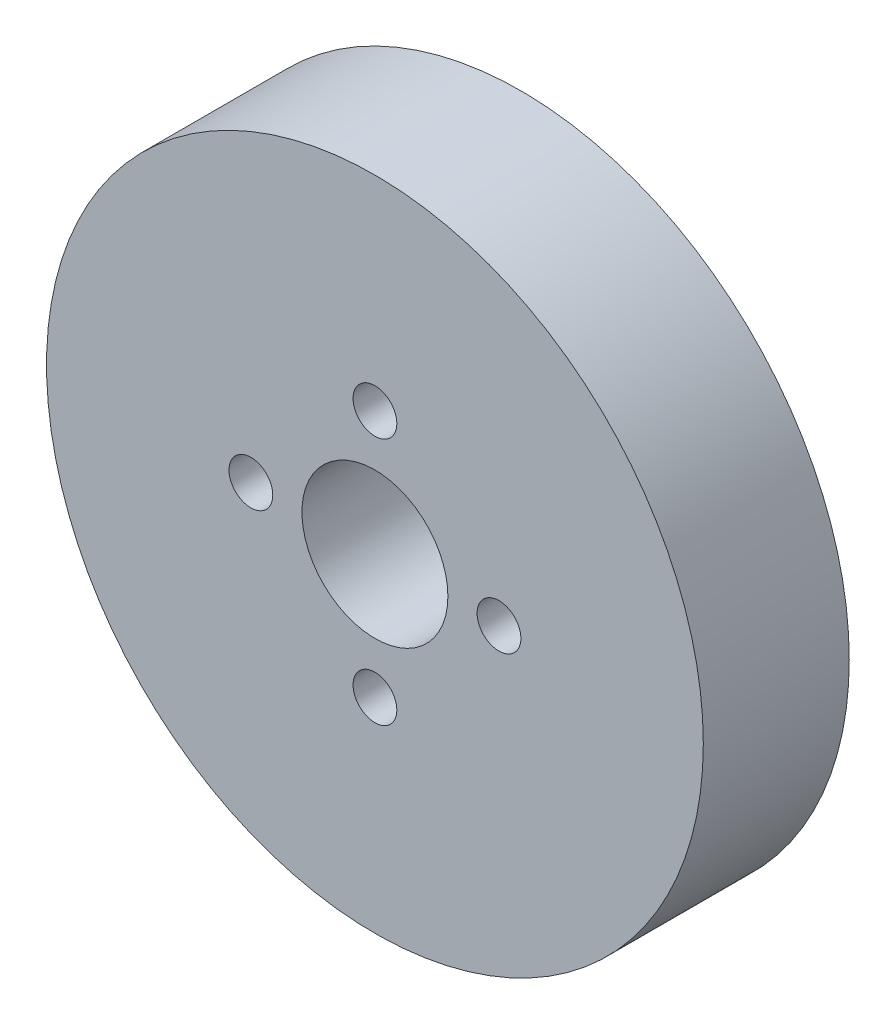
SolidWorks part; units mm, degrees
ref_plane "Plan de face" through (0, 0, 0) normal (0, 0, 1) x (1, 0, 0)
ref_plane "Plan de dessus" through (0, 0, 0) normal (0, 1, 0) x (1, 0, 0)
ref_plane "Plan de droite" through (0, 0, 0) normal (1, 0, 0) x (0, 0, -1)
sketch "Esquisse1" plane through (0, 0, 0) normal (0, 0, 1) x (1, 0, 0)
  circle A0 centre (0, 0) radius 22.5
  circle A1 centre (0, 0) radius 5
  dimension "D1" = 10
  dimension "D2" = 45
extrude "Boss.-Extru.1" add sketch "Esquisse1" along normal blind 10
hole_wizard "Dégagement M21" positions "Esquisse4" profile "Esquisse3" size "M2" standard "ISO" slot yes end condition through all
sketch "Esquisse4" plane through (0, 0, 10) normal (0, 0, 1) x (1, 0, 0)
  point P0 (0, 8.5)
  point P7 (8.5, 0)
  point P8 (0, -8.5)
  point P9 (-8.5, 0)
  point P10 (0, 0)
  dimension "D1" = 8.5
  dimension "D2" = 4
sketch "Esquisse3" plane through (0, 8.5, 10) normal (1, 0, 0) x (0, -1, 0)
  line L0 (0, 0) -> (0, 10)
  line L1 (0, 10) -> (1.5, 10)
  line L2 (1.5, 10) -> (1.5, 0)
  line L5 (1.5, 0) -> (0, 0)
  line L11 (0, -6.35) -> (0, 107.95) construction
  dimension "Diamètre du perçage jusqu'au prochain" = 3
  dimension "Profondeur du perçage jusqu'au prochain" = 10
